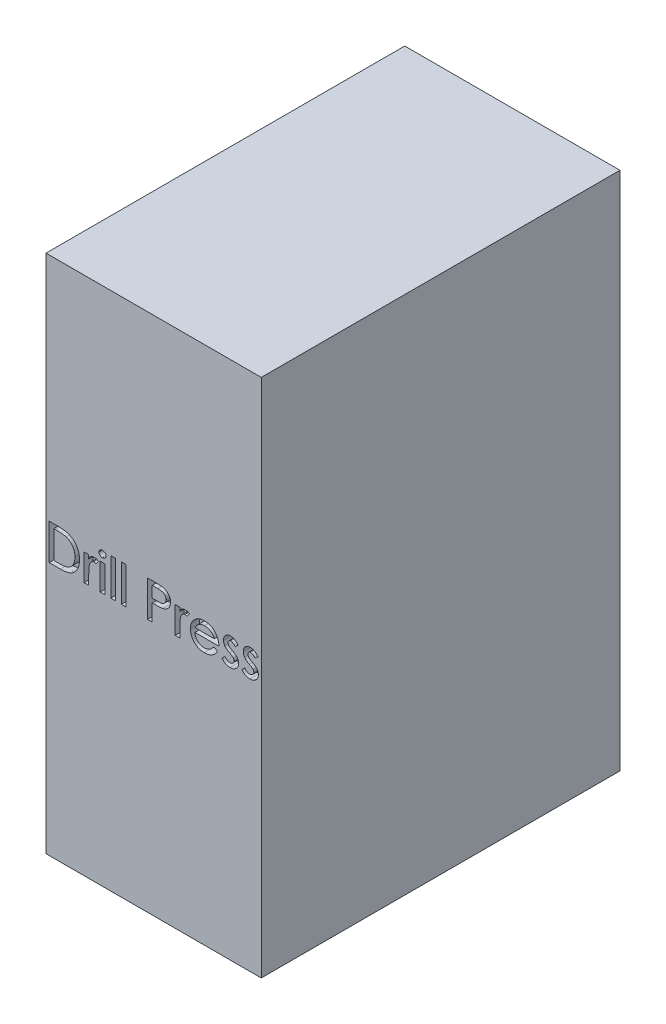
SolidWorks part; units mm, degrees
ref_plane "Front Plane" through (0, 0, 0) normal (0, 0, 1) x (1, 0, 0)
ref_plane "Top Plane" through (0, 0, 0) normal (0, 1, 0) x (1, 0, 0)
ref_plane "Right Plane" through (0, 0, 0) normal (1, 0, 0) x (0, 0, -1)
sketch "Sketch1" plane through (0, 0, 0) normal (0, 1, 0) x (1, 0, 0)
  line L1 (-152.4, -254) -> (152.4, -254)
  line L2 (-152.4, -254) -> (-152.4, 254)
  line L3 (-152.4, 254) -> (152.4, 254)
  line L4 (152.4, -254) -> (152.4, 254)
  line L5 (-152.4, -254) -> (152.4, 254) construction
  line L6 (-152.4, 254) -> (152.4, -254) construction
  point P0 (0, 0)
  dimension "D1" = 304.8
  dimension "D2" = 508
extrude "Boss-Extrude1" add sketch "Sketch1" along normal mid plane 736.6
sketch "Sketch2" [suppressed] plane through (0, 0, 203.2) normal (0, 0, 1) x (1, 0, 0)
  text T0 "<b>Band Saw</b>" font "Arial" height 50.8
extrude "Cut-Extrude1" [suppressed] cut sketch "Sketch2" against normal blind 12.7
sketch "Sketch3" plane through (0, 0, 254) normal (0, 0, 1) x (1, 0, 0)
  text T0 "<b>Drill Press</b>" font "Century Gothic" height 50.8
extrude "Cut-Extrude2" cut sketch "Sketch3" against normal blind 12.7
